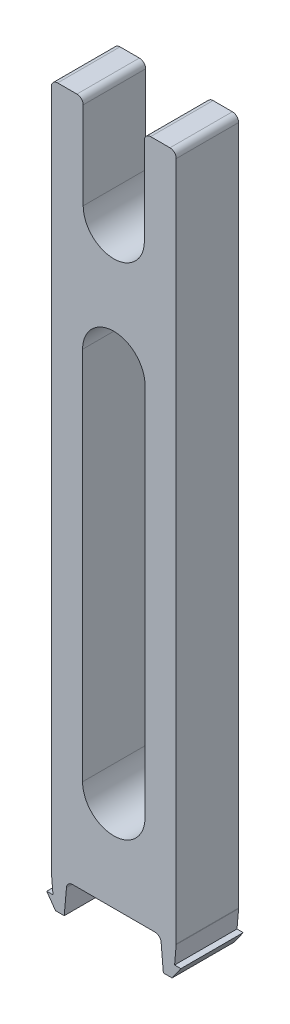
SolidWorks part; units mm, degrees
ref_plane "Front Plane" through (0, 0, 0) normal (0, 0, 1) x (1, 0, 0)
ref_plane "Top Plane" through (0, 0, 0) normal (0, 1, 0) x (1, 0, 0)
ref_plane "Right Plane" through (0, 0, 0) normal (1, 0, 0) x (0, 0, -1)
sketch "Sketch2" plane through (0, 0, 0) normal (0, 1, 0) x (1, 0, 0)
  line L1 (10, -5) -> (-10, -5)
  line L2 (10, -5) -> (10, 5)
  line L3 (10, 5) -> (-10, 5)
  line L4 (-10, -5) -> (-10, 5)
  line L5 (10, -5) -> (-10, 5) construction
  line L6 (10, 5) -> (-10, -5) construction
  point P0 (0, 0)
  dimension "D1" = 10
  dimension "D2" = 20
extrude "Boss-Extrude1" add sketch "Sketch2" along normal blind 110
sketch "Sketch3" plane through (0, 0, 5) normal (0, 0, 1) x (1, 0, 0)
  line L0 (-4.9, 110) -> (-4.9, 95)
  line L1 (-10, 110) -> (10, 110) construction
  line L2 (4.9, 95) -> (4.9, 110)
  line L3 (4.9, 110) -> (-4.9, 110)
  line L4 (-10, 0) -> (10, 0) construction
  arc A0 (-4.9, 95) -> (4.9, 95) centre (0, 95) ccw
  dimension "D2" = 4.9
  dimension "D1" = 95
extrude "Cut-Extrude1" cut sketch "Sketch3" against normal up to surface (10 mm away) up to face at (0, 55, -5)
sketch "Sketch5" plane through (0, 0, 5) normal (0, 0, 1) x (1, 0, 0)
  line L0 (0, 0) -> (0, 90.1) construction
  line L1 (-5, 15.05) -> (5, 15.05)
  line L2 (-5, 15.05) -> (-5, 75.05)
  line L3 (-5, 75.05) -> (5, 75.05)
  line L4 (5, 15.05) -> (5, 75.05)
  line L5 (-5, 15.05) -> (5, 75.05) construction
  line L6 (-5, 75.05) -> (5, 15.05) construction
  arc A0 (-5, 75.05) -> (5, 75.05) centre (0, 75.05) cw
  arc A1 (-5, 15.05) -> (5, 15.05) centre (0, 15.05) ccw
  arc A2 (-4.9, 95) -> (4.9, 95) centre (0, 95) ccw construction
  point P0 (0, 45.05)
  point P7 (0, 0)
  point P14 (0, 45.05)
  dimension "D1" = 5
  dimension "D2" = 60
extrude "Cut-Extrude2" cut sketch "Sketch5" against normal up to surface (10 mm away) contours L1 A1 | L1 L4 L3 L2 | A0 L3 up to face at (0, 78.1375, -5)
sketch "Sketch4" plane through (0, 0, 5) normal (0, 0, 1) x (1, 0, 0)
  line L0 (-10, 0) -> (-7.5, 0)
  line L1 (-10, 0) -> (10, 0) construction
  line L2 (-7.5, 0) -> (-7.9374, -5)
  line L3 (-7.9374, -5) -> (-9.3373, -5)
  line L7 (-9.3373, -5) -> (-10.7375, -3)
  line L8 (-10.7375, -3) -> (-9.7375, -3)
  line L9 (-9.7375, -3) -> (-10, 0)
  dimension "D1" = 5
  dimension "D2" = 2
  dimension "D3" = 1
  dimension "D4" = 95
  dimension "D5" = 95
  dimension "D6" = 2.5
  dimension "D7" = 124.997
extrude "Boss-Extrude2" add sketch "Sketch4" against normal up to surface (10 mm away) up to face at (0, 45.05, -5)
mirror "Mirror1" about plane through (0, 0, 0) normal (1, 0, 0) of "Boss-Extrude2"
fillet "Fillet1" radius 1 8 edges at (10, 110, 0) (4.9, 110, 0) (-4.9, 110, 0) (-10, 110, 0) (10, 0, 0) (7.5, 0, 0) (-7.5, 0, 0) (-10, 0, 0)
